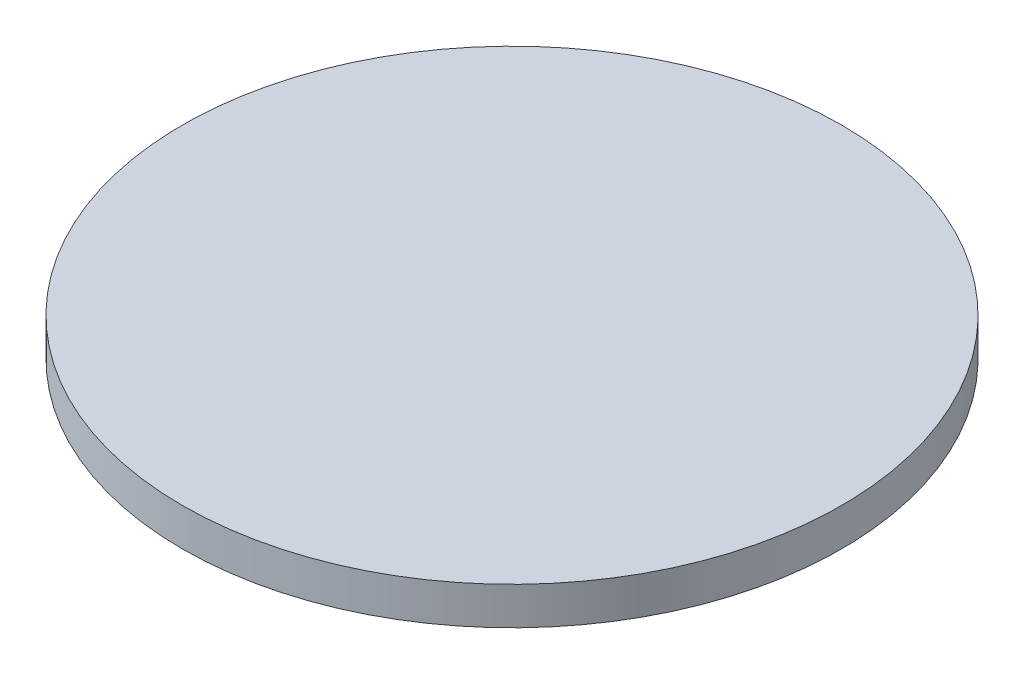
SolidWorks part; units mm, degrees
material "ABS"
ref_plane "Front Plane" through (0, 0, 0) normal (0, 0, 1) x (1, 0, 0)
ref_plane "Top Plane" through (0, 0, 0) normal (0, 1, 0) x (1, 0, 0)
ref_plane "Right Plane" through (0, 0, 0) normal (1, 0, 0) x (0, 0, -1)
sketch "Sketch3" plane through (0, 0, 0) normal (0, 1, 0) x (1, 0, 0)
  circle A0 centre (0, 0) radius 175
extrude "Boss-Extrude1" add sketch "Sketch3" along normal blind 20
sketch "Sketch4" plane through (0, 0, 0) normal (0, -1, 0) x (1, 0, 0)
  circle A0 centre (0, 0) radius 70
extrude "Cut-Extrude1" cut sketch "Sketch4" against normal blind 10
